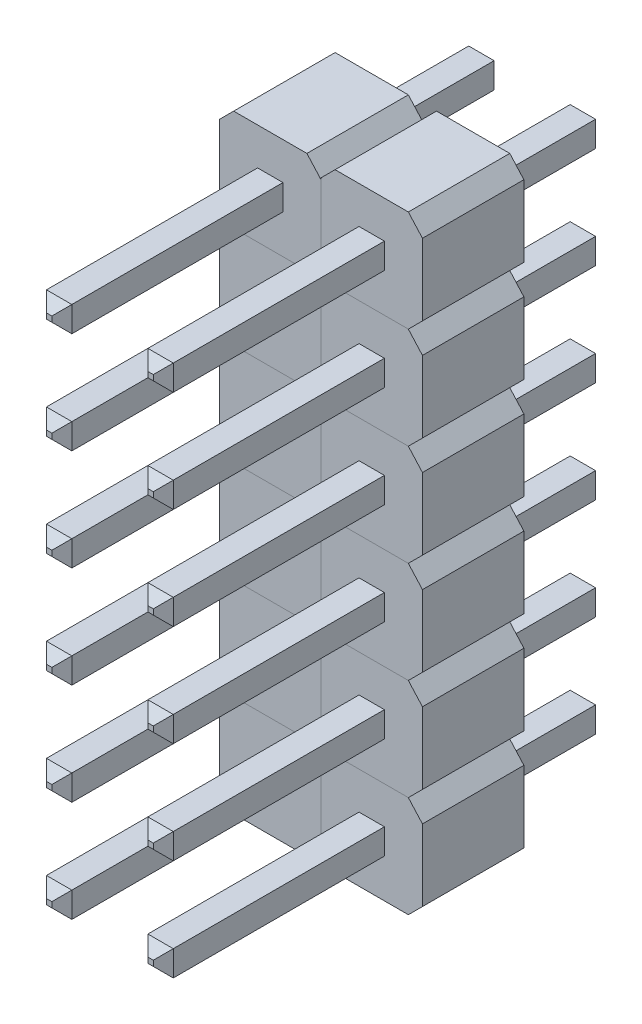
SolidWorks part; units mm, degrees
ref_plane "Alzado" through (0, 0, 0) normal (0, 0, 1) x (1, 0, 0)
ref_plane "Planta" through (0, 0, 0) normal (0, 1, 0) x (1, 0, 0)
ref_plane "Vista lateral" through (0, 0, 0) normal (1, 0, 0) x (0, 0, -1)
sketch "pin_drawing" plane through (0, 0, 0) normal (0, 0, 1) x (1, 0, 0)
  line B0 (-0.318, 0.318) -> (-1.2705, 0.318) construction
  line B1 (-0.9169, 1.25) -> (0.9169, 1.25)
  line B2 (-1.2705, 0.8964) -> (-1.2705, -0.8964)
  line B3 (-1.2705, 0.8964) -> (-0.9169, 1.25)
  line B4 (0.318, -0.318) -> (1.2705, -0.318) construction
  line B5 (-0.318, -0.318) -> (0.318, 0.318) construction
  line B6 (1.2705, 0.8564) -> (1.2705, -0.9364)
  line B7 (-0.318, 0) -> (-0.318, 0.318) construction
  line B8 (1.2705, -0.9364) -> (0.9169, -1.29)
  line B9 (0.9169, 1.25) -> (1.2705, 0.8564)
  line B10 (0.318, 0) -> (0.318, -0.318) construction
  line B11 (-0.9169, -1.29) -> (-1.2705, -0.8964)
  line B12 (-0.318, 0.318) -> (0.318, 0.318)
  line B13 (-0.318, 0.318) -> (-0.318, -0.318)
  line B14 (-0.318, -0.318) -> (0.318, -0.318)
  line B15 (0.318, 0.318) -> (0.318, -0.318)
  line B16 (0, 0) -> (0.318, -0.318) construction
  line B17 (0, 0) -> (-0.318, 0.318) construction
  line B18 (0.9169, -1.29) -> (-0.9169, -1.29)
sketch_block_instance "Block1-1"
sketch_block "Block1" parameters "D1"=0.318, "D2"=0.9525, "D3"=0.5, "D4"=135, "D5"=0.5, "D6"=135, "D7"=2.54, "D8"=2.541
extrude "Boss-Extrude1" add sketch "pin_drawing" along normal blind 2.54
sketch "Sketch1" plane through (0, 0, 2.54) normal (0, 0, 1) x (1, 0, 0)
  line L0 (-0.318, 0.318) -> (-0.318, -0.318) construction
  line L1 (0.318, -0.318) -> (0.318, 0.318) construction
  line L2 (0.318, 0.318) -> (-0.318, 0.318) construction
  line L3 (-0.318, -0.318) -> (0.318, -0.318) construction
  line L4 (0.318, -0.318) -> (0.318, 0.318)
  line L5 (0.318, 0.318) -> (-0.318, 0.318)
  line L6 (-0.318, -0.318) -> (0.318, -0.318)
  line L7 (-0.318, 0.318) -> (-0.318, -0.318)
extrude "Boss-Extrude2" add sketch "Sketch1" along normal blind 5.5372 and the other way blind 5.5372 separate body
chamfer "Chamfer1" distance 0.25 angle 45 8 edges at (0.318, 0, -2.9972) (0, 0.318, -2.9972) (-0.318, 0, -2.9972) (0, -0.318, -2.9972) (-0.318, 0, 8.0772) (0, 0.318, 8.0772) (0.318, 0, 8.0772) (0, -0.318, 8.0772)
pattern_linear "LPattern2" count 6 spacing 2.54 along (0, -1, 0) count 2 spacing 2.54 along (1, 0, 0) of bodies 105 103
